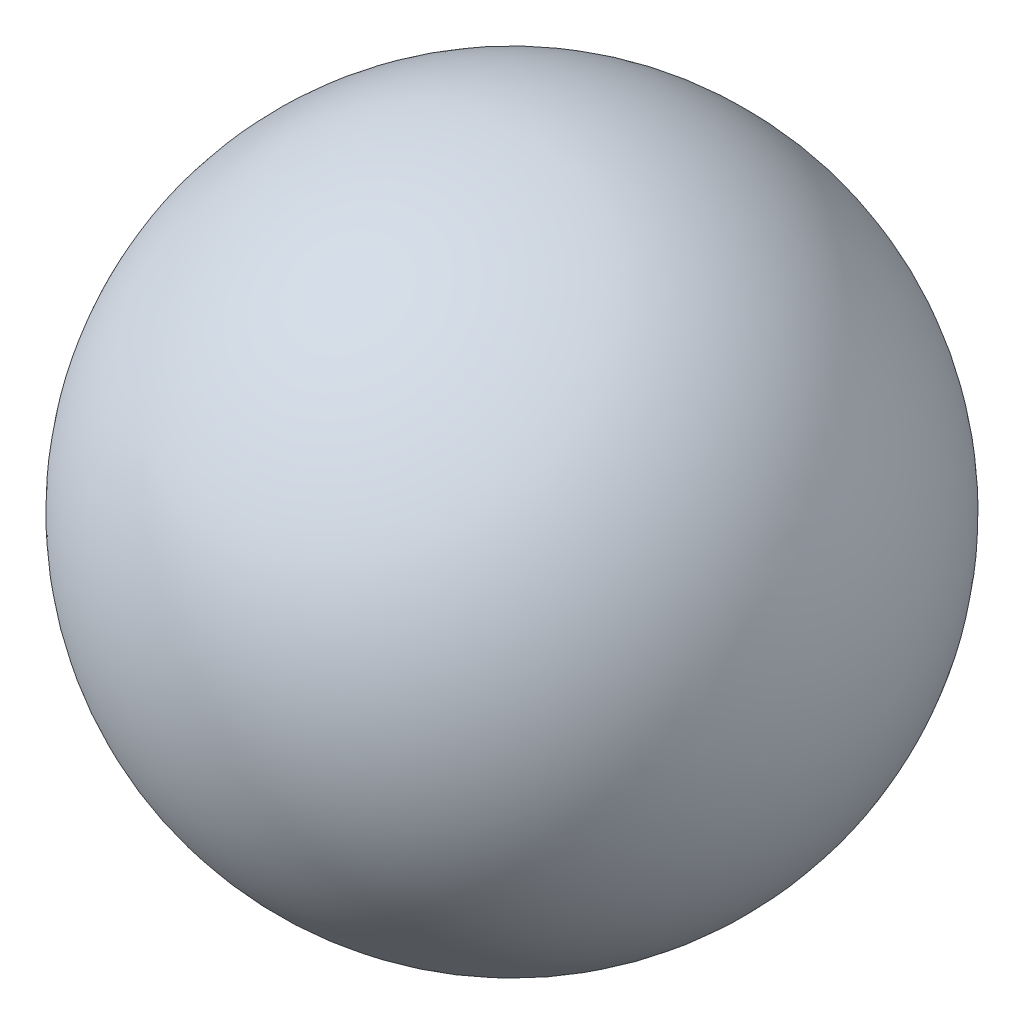
SolidWorks part; units mm, degrees
ref_plane "Alzado" through (0, 0, 0) normal (0, 0, 1) x (1, 0, 0)
ref_plane "Planta" through (0, 0, 0) normal (0, 1, 0) x (1, 0, 0)
ref_plane "Vista lateral" through (0, 0, 0) normal (1, 0, 0) x (0, 0, -1)
ref_plane "Plano1" through (0, 0, 0) normal (0, 0, 1) x (1, 0, 0)
sketch "Croquis1" plane through (0, 0, 0) normal (0, 0, 1) x (1, 0, 0)
  line L0 (3.969, 16.75) -> (-3.969, 16.75)
  line L1 (3.969, 16.75) -> (-3.969, 16.75) construction
  arc A0 (-3.969, 16.75) -> (3.969, 16.75) centre (0, 16.75) cw
revolve "Revolución1" add sketch "Croquis1" angle 360 about L1
